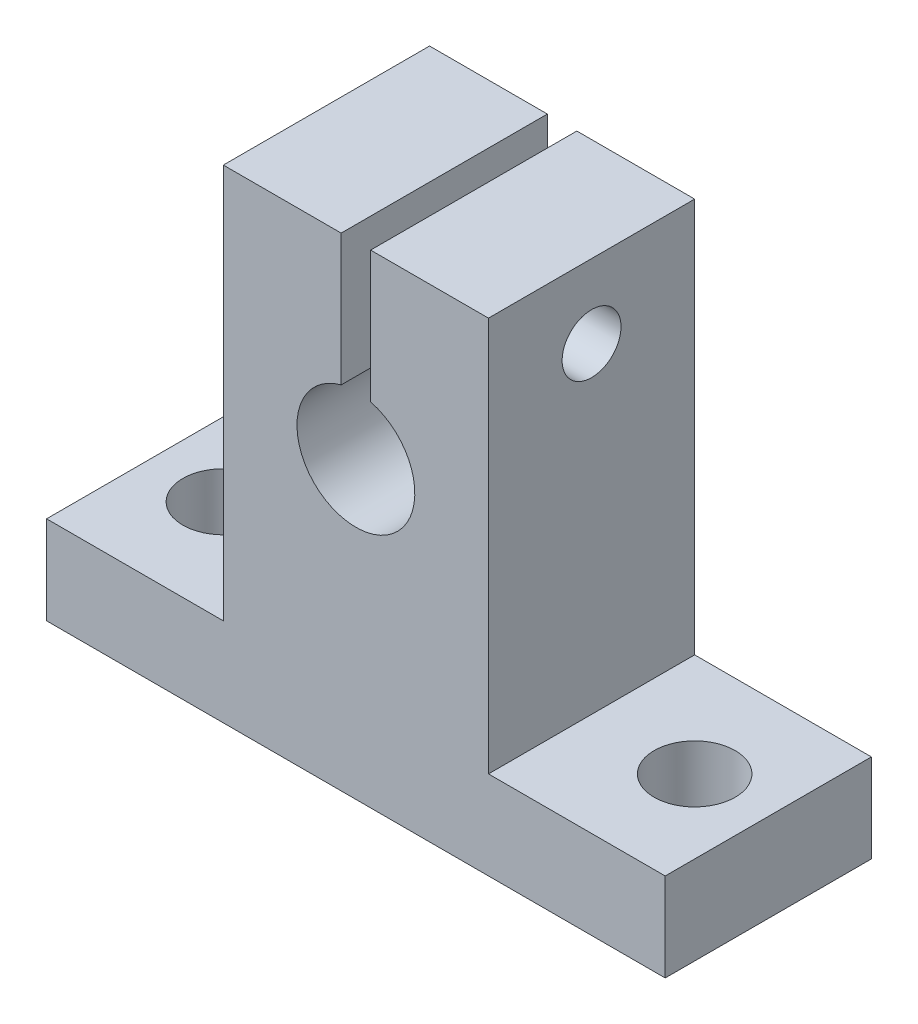
SolidWorks part; units mm, degrees
ref_plane "前视基准面" through (0, 0, 0) normal (0, 0, 1) x (1, 0, 0)
ref_plane "上视基准面" through (0, 0, 0) normal (0, 1, 0) x (1, 0, 0)
ref_plane "右视基准面" through (0, 0, 0) normal (1, 0, 0) x (0, 0, -1)
sketch "草图1" plane through (0, 0, 0) normal (0, 0, 1) x (1, 0, 0)
  line L0 (21, 0) -> (-21, 0)
  line L1 (-21, 0) -> (-21, 6)
  line L2 (9, 6) -> (9, 32.8)
  line L3 (0, 0) -> (0, 6) construction
  line L4 (-21, 6) -> (-9, 6)
  line L5 (-9, 6) -> (-9, 32.8)
  line L6 (-9, 32.8) -> (9, 32.8)
  line L7 (21, 6) -> (9, 6)
  line L8 (21, 0) -> (21, 6)
  point P10 (0, 32.8)
  point P13 (0, 0)
  dimension "D1" = 21
  dimension "D2" = 6
  dimension "D3" = 32.8
  dimension "D4" = 9
extrude "凸台-拉伸1" add sketch "草图1" along normal blind 14
sketch "草图2" plane through (0, 0, 0) normal (0, 0, -1) x (-1, 0, 0)
  line L0 (0, 32.8) -> (0, 0) construction
  line L1 (-9, 32.8) -> (9, 32.8) construction
  line L2 (21, 0) -> (-21, 0) construction
  line L3 (-1, 23.873) -> (-1, 32.8)
  line L4 (-9, 6) -> (-9, 32.8) construction
  line L5 (1, 23.873) -> (1, 32.8)
  line L6 (-1, 32.8) -> (1, 32.8)
  line L7 (1, 23.873) -> (-1, 23.873)
  circle A0 centre (0, 20) radius 4
  dimension "D1" = 8
  dimension "D2" = 20
  dimension "D3" = 8
extrude "切除-拉伸2" cut sketch "草图2" against normal blind 14 contours L0 L7 A0 | L7 L0 A0
sketch "草图4" plane through (0, 0, 0) normal (0, -1, 0) x (1, 0, 0)
  line L0 (0, 0) -> (0, 14) construction
  line L1 (-21, 14) -> (21, 14) construction
  line L2 (21, 7) -> (-21, 7) construction
  line L3 (21, 14) -> (21, 0) construction
  line L4 (-21, 14) -> (-21, 0) construction
  circle A0 centre (16, 7) radius 2.75
  circle A1 centre (-16, 7) radius 2.75
  dimension "D1" = 5.5
  dimension "D2" = 16
extrude "切除-拉伸3" cut sketch "草图4" against normal up to next
sketch "草图5" plane through (-9, 0, 0) normal (-1, 0, 0) x (0, 0, 1)
  line L0 (7, 32.8) -> (7, 6) construction
  line L1 (14, 32.8) -> (0, 32.8) construction
  line L2 (14, 6) -> (0, 6) construction
  circle A0 centre (7, 27.8) radius 2
  dimension "D1" = 4
  dimension "D2" = 5
extrude "切除-拉伸4" cut sketch "草图5" against normal up to surface (18 mm away) up to face at (9, 19.4, 7)
sketch "草图6" plane through (-9, 0, 0) normal (-1, 0, 0) x (0, 0, 1)
  circle A0 centre (7, 27.8) radius 3.5
  dimension "D1" = 7
extrude "切除-拉伸5" cut sketch "草图6" against normal blind 4
